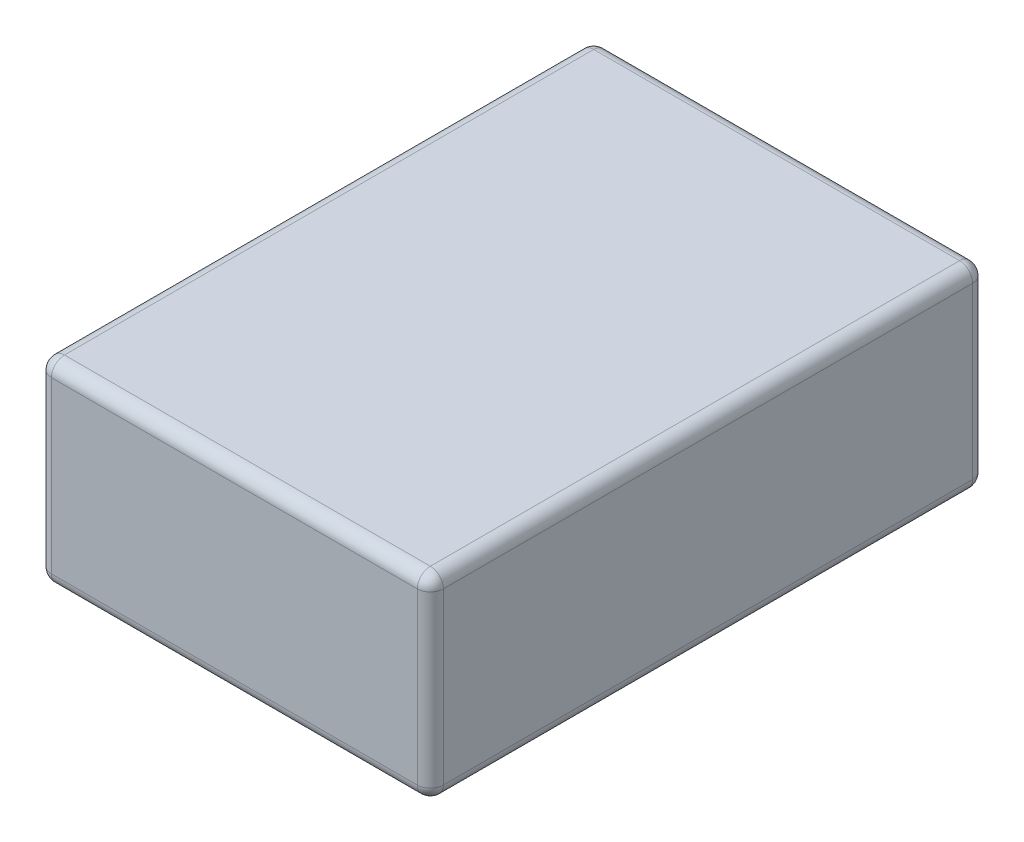
SolidWorks part; units mm, degrees
ref_plane "前视基准面" through (0, 0, 0) normal (0, 0, 1) x (1, 0, 0)
ref_plane "上视基准面" through (0, 0, 0) normal (0, 1, 0) x (1, 0, 0)
ref_plane "右视基准面" through (0, 0, 0) normal (1, 0, 0) x (0, 0, -1)
sketch "草图1" plane through (0, 0, 0) normal (0, 1, 0) x (1, 0, 0)
  line L1 (-28, 42.5) -> (28, 42.5)
  line L2 (-30, 40.5) -> (-30, -40.5)
  line L3 (-28, -42.5) -> (28, -42.5)
  line L4 (30, 40.5) -> (30, -40.5)
  line L5 (0, -55) -> (0, 55) construction
  line L6 (-55, 0) -> (55, 0) construction
  arc A0 (-30, -40.5) -> (-28, -42.5) centre (-28, -40.5) ccw
  arc A1 (28, -42.5) -> (30, -40.5) centre (28, -40.5) ccw
  arc A2 (30, 40.5) -> (28, 42.5) centre (28, 40.5) ccw
  arc A3 (-30, 40.5) -> (-28, 42.5) centre (-28, 40.5) cw
  dimension "D5" = 2
  dimension "D1" = 30
  dimension "D2" = 30
  dimension "D3" = 42.5
  dimension "D4" = 42.5
extrude "凸台-拉伸1" add sketch "草图1" along normal blind 30
fillet "圆角1" radius 2 16 edges at (0, 0, 42.5) (29.4142, 0, 41.9142) (30, 0, 0) (29.4142, 0, -41.9142) (0, 0, -42.5) (-29.4142, 0, -41.9142) (-30, 0, 0) (-29.4142, 0, 41.9142) (-30, 30, 0) (-29.4142, 30, -41.9142) (0, 30, -42.5) (29.4142, 30, -41.9142) (30, 30, 0) (29.4142, 30, 41.9142) (0, 30, 42.5) (-29.4142, 30, 41.9142)
